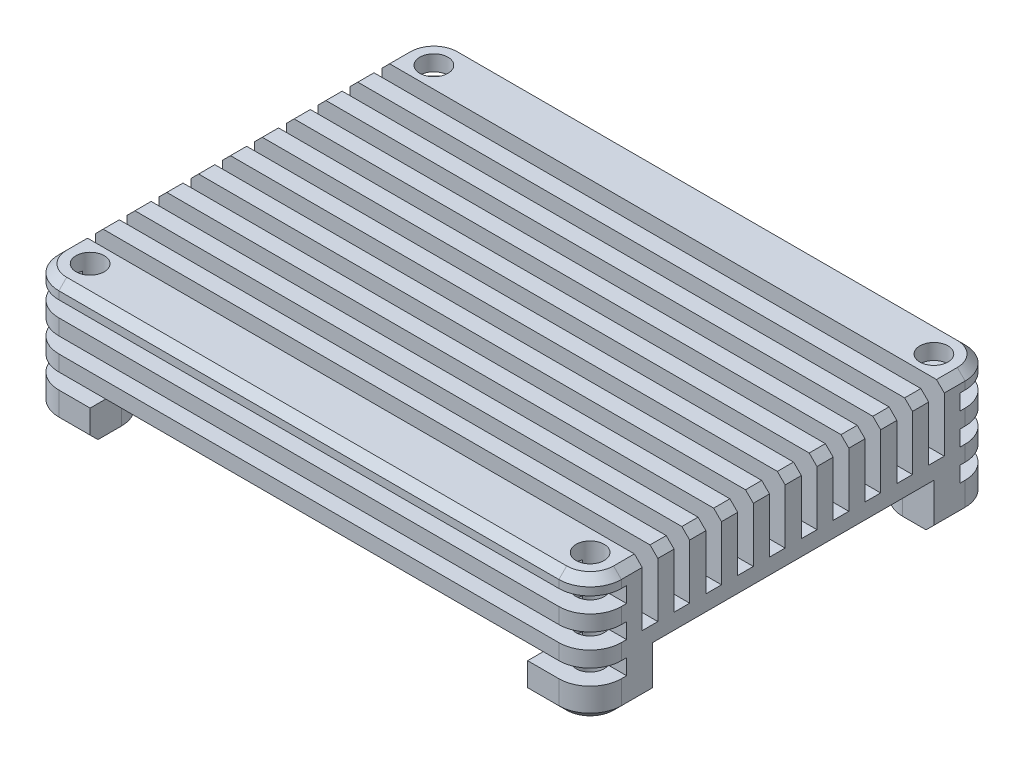
SolidWorks part; units mm, degrees
ref_plane "Plan de face" through (0, 0, 0) normal (0, 0, 1) x (1, 0, 0)
ref_plane "Plan de dessus" through (0, 0, 0) normal (0, 1, 0) x (1, 0, 0)
ref_plane "Plan de droite" through (0, 0, 0) normal (1, 0, 0) x (0, 0, -1)
sketch "Esquisse1" plane through (0, 0, 0) normal (0, 1, 0) x (1, 0, 0)
  line L1 (-27, -19.5) -> (27, -19.5)
  line L2 (-27, -19.5) -> (-27, 19.5)
  line L3 (-27, 19.5) -> (27, 19.5)
  line L4 (27, -19.5) -> (27, 19.5)
  line L5 (-27, -19.5) -> (27, 19.5) construction
  line L6 (-27, 19.5) -> (27, -19.5) construction
  point P0 (0, 0)
  dimension "D1" = 54
  dimension "D2" = 39
extrude "Boss.-Extru.1" add sketch "Esquisse1" along normal blind 12
fillet "Congé1" radius 3 4 edges at (27, 6, -19.5) (27, 6, 19.5) (-27, 6, -19.5) (-27, 6, 19.5)
chamfer "Chanfrein1" distance 0.75 angle 45 16 edges at (26.1213, 12, 18.6213) (0, 12, 19.5) (-26.1213, 12, 18.6213) (-27, 12, 0) (-26.1213, 12, -18.6213) (0, 12, -19.5) (26.1213, 12, -18.6213) (27, 12, 0) (-26.1213, 0, -18.6213) (-27, 0, 0) (-26.1213, 0, 18.6213) (0, 0, 19.5) (26.1213, 0, 18.6213) (27, 0, 0) (26.1213, 0, -18.6213) (0, 0, -19.5)
sketch "Esquisse2" plane through (-27, 0, 0) normal (-1, 0, 0) x (0, 0, 1)
  line L0 (-16.5, 12) -> (16.5, 12) construction
  line L1 (-14.5, 6) -> (-13, 6)
  line L2 (-14.5, 6) -> (-14.5, 12)
  line L3 (-14.5, 12) -> (-13, 12)
  line L4 (-13, 6) -> (-13, 12)
  line L5 (16.5, 0) -> (-16.5, 0) construction
  line L6 (-19.5, 0.75) -> (-19.5, 11.25) construction
  line L7 (14.5, 0) -> (14.5, 5.5676) construction
  line L8 (-14.5, 6) -> (-19.5, 6) construction
  line L9 (14.5, 5.5676) -> (19.5, 5.5676) construction
  line L10 (19.5, 11.25) -> (19.5, 0.75) construction
  dimension "D1" = 1.5
  dimension "D2" = 6
  dimension "D3" = 5
extrude "Enlèv. mat.-Extru.1" cut sketch "Esquisse2" against normal through all
sketch "Esquisse3" plane through (-27, 0, 0) normal (-1, 0, 0) x (0, 0, 1)
  line L0 (-19.5, 0.75) -> (-19.5, 11.25) construction
  line L1 (-19.5, 10.5) -> (-16, 10.5)
  line L2 (-19.5, 10.5) -> (-19.5, 9)
  line L3 (-19.5, 9) -> (-16, 9)
  line L4 (-16, 10.5) -> (-16, 9)
  line L5 (-14.5, 6) -> (-13, 6) construction
  line L6 (-16, 9) -> (-14.5, 9) construction
  line L7 (-14.5, 11.25) -> (-14.5, 6) construction
  line L8 (-16, 10.5) -> (-16, 12) construction
  line L9 (-16.5, 12) -> (-14.5, 12) construction
  line L10 (-19.5, 7.5) -> (-19.5, 6)
  line L11 (-19.5, 7.5) -> (-16, 7.5)
  line L12 (-16, 7.5) -> (-16, 6)
  line L13 (-19.5, 6) -> (-16, 6)
  line L14 (-19.5, 4.5) -> (-19.5, 3)
  line L15 (-19.5, 4.5) -> (-16, 4.5)
  line L16 (-16, 4.5) -> (-16, 3)
  line L17 (-19.5, 3) -> (-16, 3)
  dimension "D1" = 3
extrude "Enlèv. mat.-Extru.2" cut sketch "Esquisse3" against normal through all
mirror "Symétrie1" about plane through (0, 0, 0) normal (0, 0, 1) of "Enlèv. mat.-Extru.2", "Enlèv. mat.-Extru.1"
pattern_linear "Répétition linéaire1" count 10 spacing 3.0556 along (0, 0, 1) of "Enlèv. mat.-Extru.1"
sketch "Esquisse4" plane through (0, 12, 0) normal (0, 1, 0) x (1, 0, 0)
  line L1 (-24, -16.5) -> (24, -16.5) construction
  line L2 (-24, -16.5) -> (-24, 16.5) construction
  line L3 (-24, 16.5) -> (24, 16.5) construction
  line L4 (24, -16.5) -> (24, 16.5) construction
  line L5 (-24, -16.5) -> (24, 16.5) construction
  line L6 (-24, 16.5) -> (24, -16.5) construction
  circle A0 centre (-24, 16.5) radius 1.35
  circle A1 centre (24, 16.5) radius 1.35
  circle A2 centre (24, -16.5) radius 1.35
  circle A3 centre (-24, -16.5) radius 1.35
  point P0 (0, 0)
  dimension "D1" = 2.7
  dimension "D2" = 33
  dimension "D3" = 48
extrude "Enlèv. mat.-Extru.3" cut sketch "Esquisse4" against normal through all
sketch "Esquisse5" plane through (0, 0, 0) normal (0, -1, 0) x (1, 0, 0)
  line L0 (-24, 13.5) -> (-27, 13.5)
  line L1 (-27, -16.5) -> (-27, 16.5) construction
  line L2 (-27, 13.5) -> (-27, -13.5)
  line L3 (-27, -13.5) -> (-24, -13.5)
  line L4 (-21, -16.5) -> (-21, -19.5)
  line L5 (24, -19.5) -> (-24, -19.5) construction
  line L6 (-21, -19.5) -> (21, -19.5)
  line L7 (21, -19.5) -> (21, -16.5)
  line L8 (24, -13.5) -> (27, -13.5)
  line L9 (27, 16.5) -> (27, -16.5) construction
  line L10 (27, -13.5) -> (27, 13.5)
  line L11 (27, 13.5) -> (24, 13.5)
  line L12 (-21, 16.5) -> (-21, 19.5)
  line L13 (-24, 19.5) -> (24, 19.5) construction
  line L14 (-21, 19.5) -> (21, 19.5)
  line L15 (21, 19.5) -> (21, 16.5)
  arc A0 (-24, 13.5) -> (-21, 16.5) centre (-24, 16.5) ccw
  arc A1 (21, 16.5) -> (24, 13.5) centre (24, 16.5) ccw
  arc A2 (24, -13.5) -> (21, -16.5) centre (24, -16.5) ccw
  arc A3 (-21, -16.5) -> (-24, -13.5) centre (-24, -16.5) ccw
  arc A4 (-24, 19.5) -> (-27, 16.5) centre (-24, 16.5) ccw construction
extrude "Enlèv. mat.-Extru.4" cut sketch "Esquisse5" against normal blind 4.5
